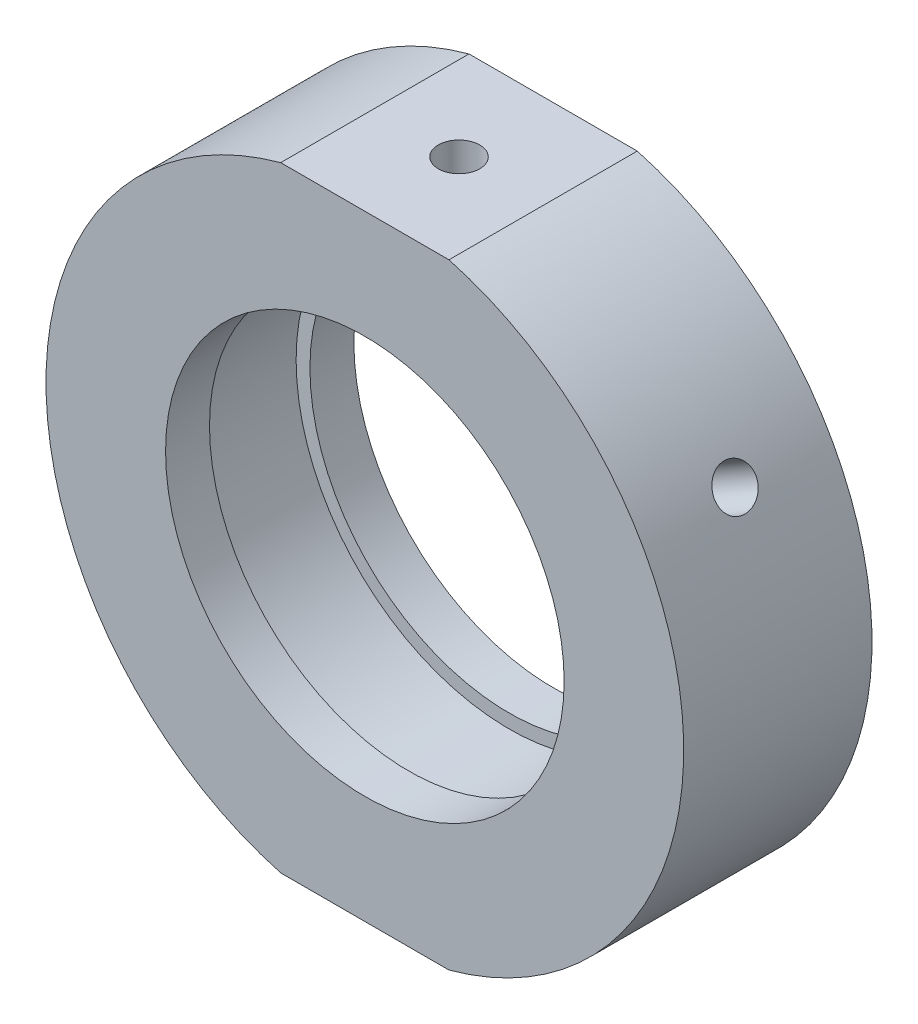
SolidWorks part; units mm, degrees
ref_plane "前视基准面" through (0, 0, 0) normal (0, 0, 1) x (1, 0, 0)
ref_plane "上视基准面" through (0, 0, 0) normal (0, 1, 0) x (1, 0, 0)
ref_plane "右视基准面" through (0, 0, 0) normal (1, 0, 0) x (0, 0, -1)
sketch "草图1" plane through (0, 0, 0) normal (0, 1, 0) x (1, 0, 0)
  line L0 (0, 31.9391) -> (0, -26.491) construction
  line L1 (25.4, 7.5) -> (25.4, -7.5)
  line L6 (25.4, -7.5) -> (15.875, -7.5)
  line L7 (15.875, -7.5) -> (15.875, -4)
  line L8 (15.875, -4) -> (16.975, -4)
  line L9 (16.975, -4) -> (16.975, 4)
  line L10 (16.975, 4) -> (15.875, 4)
  line L11 (15.875, 4) -> (15.875, 7.5)
  line L12 (15.875, 7.5) -> (25.4, 7.5)
  line L17 (19.05, 0) -> (-5.0345, 0) construction
  point P6 (16.975, 0)
  dimension "D2" = 16.975
  dimension "D3" = 15.875
  dimension "D4" = 15.875
  dimension "D5" = 15
  dimension "D6" = 3.5
  dimension "D7" = 7.5
  dimension "D9" = 25.4
  dimension "D14" = 8
  dimension "D15" = 4
  dimension "D18" = 0
revolve "旋转1" add sketch "草图1" angle 360 about L0
sketch "草图2" plane through (0, 0, 7.5) normal (0, 0, 1) x (1, 0, 0)
  line L0 (0, 0) -> (43.1523, 0) construction
  line L1 (-33.152, 33.7489) -> (30.8698, 33.7489)
  line L2 (-33.152, 33.7489) -> (-33.152, 24.5)
  line L3 (-33.152, 24.5) -> (30.8698, 24.5)
  line L4 (30.8698, 33.7489) -> (30.8698, 24.5)
  line L5 (30.8698, -33.7489) -> (30.8698, -24.5)
  line L6 (-33.152, -24.5) -> (30.8698, -24.5)
  line L7 (-33.152, -33.7489) -> (-33.152, -24.5)
  line L8 (-33.152, -33.7489) -> (30.8698, -33.7489)
  dimension "D1" = 24.5
extrude "切除-拉伸1" cut sketch "草图2" against normal blind 49
sketch "草图10" plane through (0, 0, 0) normal (0, 0, 1) x (1, 0, 0)
  line L0 (0, 24.5) -> (0, -24.5)
  line L1 (-6.7015, 24.5) -> (6.7015, 24.5) construction
  line L2 (-6.7015, -24.5) -> (6.7015, -24.5) construction
  line L3 (0, 0) -> (-21.997, 12.7)
  line L4 (0, 0) -> (21.997, 12.7)
  arc A2 (6.7015, -24.5) -> (6.7015, 24.5) centre (0, 0) ccw construction
  arc A3 (-6.7015, 24.5) -> (-6.7015, -24.5) centre (0, 0) ccw construction
  arc A4 (21.997, 12.7) -> (6.7015, 24.5) centre (0, 0) ccw
  arc A5 (-6.7015, 24.5) -> (-21.997, 12.7) centre (0, 0) ccw
  dimension "D1" = 60
  dimension "D2" = 60
hole_wizard "M4 螺纹孔2" positions "草图15" profile "草图16" tap size "M4" standard "ISO"
sketch "草图15" plane through (0, 24.5, 0) normal (0, 1, 0) x (1, 0, 0)
  point P0 (0, 0)
sketch "草图16" plane through (0, 24.5, 0) normal (1, 0, 0) x (0, 0, 1)
  line L0 (0, 0) -> (0, 6.4914)
  line L1 (0, 6.4914) -> (1.65, 5.5)
  line L2 (1.65, 5.5) -> (1.65, 0)
  line L5 (1.65, 0) -> (0, 0)
  line L10 (0, 6.4914) -> (-1.65, 5.5) construction
  line L11 (0, -6.35) -> (0, 107.95) construction
  dimension "螺纹孔钻头直径" = 3.3
  dimension "螺纹孔钻头深度" = 5.5
  dimension "导头角度" = 118
cosmetic thread "孔螺蚊线1" parameters "D1"=5.5, "D2"=4
hole_wizard "M6 螺纹孔2" positions "草图17" profile "草图18" tap size "M6" standard "ISO"
sketch "草图17" plane through (0, -24.5, 0) normal (0, -1, 0) x (-1, 0, 0)
  point P0 (0, 0)
sketch "草图18" plane through (0, -24.5, 0) normal (1, 0, 0) x (0, 0, -1)
  line L0 (0, 0) -> (0, 7.0022)
  line L1 (0, 7.0022) -> (2.5, 5.5)
  line L2 (2.5, 5.5) -> (2.5, 0)
  line L5 (2.5, 0) -> (0, 0)
  line L10 (0, 7.0022) -> (-2.5, 5.5) construction
  line L11 (0, -6.35) -> (0, 107.95) construction
  dimension "螺纹孔钻头直径" = 5
  dimension "螺纹孔钻头深度" = 5.5
  dimension "导头角度" = 118
cosmetic thread "孔螺蚊线2" parameters "D1"=5.5, "D2"=6
hole_wizard "M4 螺纹孔3" positions "3D草图4" profile "草图22" tap size "M4" standard "ISO"
sketch3d "3D草图4"
  point P0 (-21.997, 12.7, 0)
  point P4 (21.997, 12.7, 0)
  point P7 (21.997, 12.7, 0)
  point P11 (-21.997, 12.7, 0)
  point P15 (21.997, 12.7, 0)
  point P17 (21.997, 12.7, 0)
sketch "草图22" plane through (21.997, 12.7, 0) normal (0, 0, 1) x (-0.5, 0.866, 0)
  line L0 (0, 0) -> (0, 14.3914)
  line L1 (0, 14.3914) -> (1.65, 13.4)
  line L2 (1.65, 13.4) -> (1.65, 0)
  line L5 (1.65, 0) -> (0, 0)
  line L10 (0, 14.3914) -> (-1.65, 13.4) construction
  line L11 (0, -6.35) -> (0, 107.95) construction
  dimension "螺纹孔钻头直径" = 3.3
  dimension "螺纹孔钻头深度" = 13.4
  dimension "导头角度" = 118
cosmetic thread "孔螺蚊线4" parameters "D1"=8.0514, "D2"=4
cosmetic thread "孔螺蚊线5" parameters "D1"=8.0514, "D2"=4
